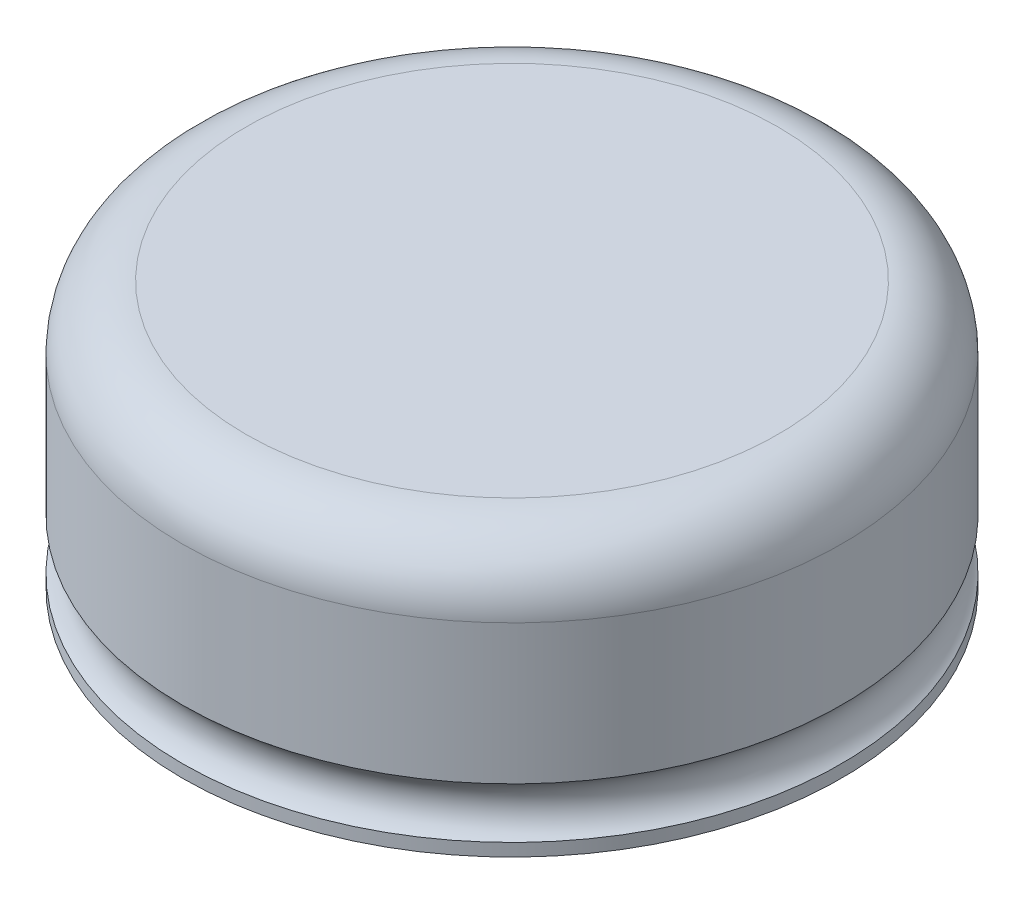
SolidWorks part; units mm, degrees
ref_plane "前视基准面" through (0, 0, 0) normal (0, 0, 1) x (1, 0, 0)
ref_plane "上视基准面" through (0, 0, 0) normal (0, 1, 0) x (1, 0, 0)
ref_plane "右视基准面" through (0, 0, 0) normal (1, 0, 0) x (0, 0, -1)
sketch "草图1" plane through (0, 0, 0) normal (0, 0, 1) x (1, 0, 0)
  line L0 (0, 0) -> (0, -26192.4691) construction
  line L1 (0, 0) -> (26, 0)
  line L2 (26, 0) -> (26, 1)
  line L3 (0, 0) -> (0, 6)
  line L4 (0, 6) -> (26, 6)
  line L5 (26, 6) -> (26, 5)
  arc A0 (26, 5) -> (26, 1) centre (27.5, 3) ccw
  point P8 (26, 5.8917)
  dimension "D1" = 2.5
  dimension "D2" = 26
  dimension "D3" = 6
  dimension "D4" = 1
revolve "旋转1" add sketch "草图1" angle 360 about L0
sketch "草图2" plane through (0, 6, 0) normal (0, 1, 0) x (1, 0, 0)
  circle A0 centre (0, 0) radius 26
  dimension "D1" = 52
extrude "凸台-拉伸1" add sketch "草图2" along normal blind 15
fillet "圆角1" radius 5 1 edges at (0, 21, 26)
